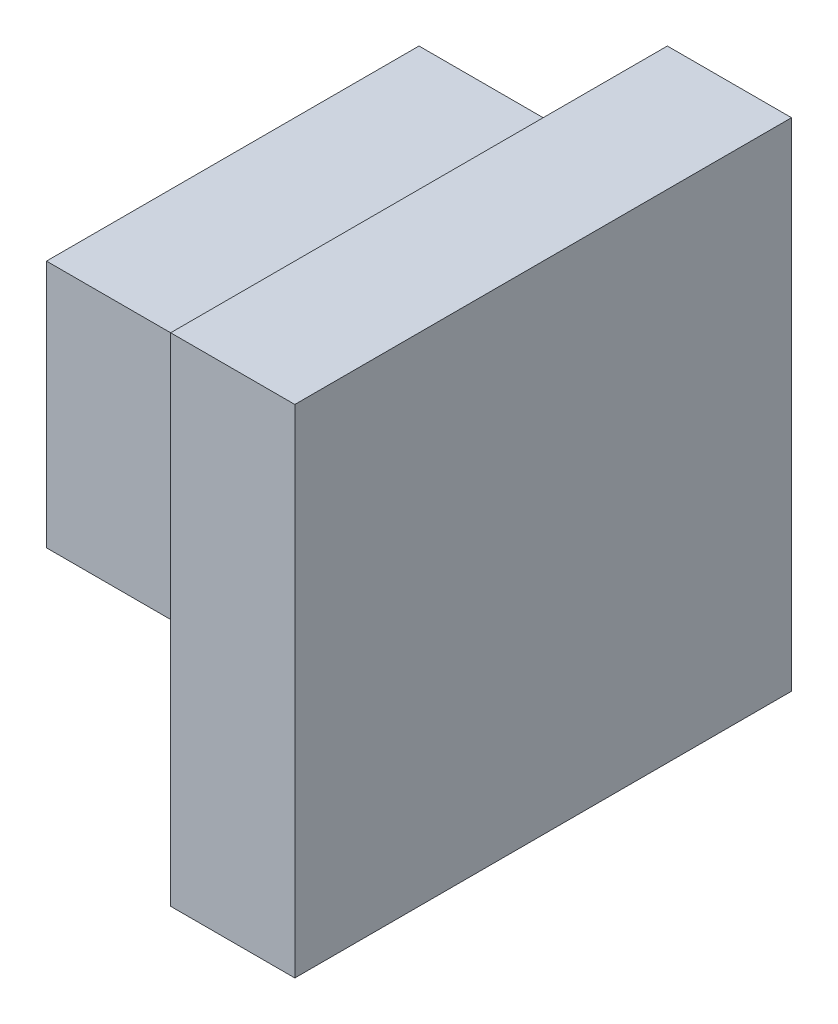
SolidWorks part; units mm, degrees
ref_plane "Front" through (0, 0, 0) normal (0, 0, 1) x (1, 0, 0)
ref_plane "Top" through (0, 0, 0) normal (0, 1, 0) x (1, 0, 0)
ref_plane "Right" through (0, 0, 0) normal (1, 0, 0) x (0, 0, -1)
sketch "Sketch1" plane through (0, 0, 0) normal (0, 0, 1) x (1, 0, 0)
  line L0 (0, 0) -> (0, 2)
  line L1 (0, 2) -> (1, 2)
  line L2 (1, 2) -> (1, 3)
  line L3 (1, 3) -> (3, 3)
  line L4 (3, 3) -> (3, 4)
  line L5 (3, 4) -> (4, 4)
  line L6 (4, 4) -> (4, 0)
  line L7 (4, 0) -> (3, 0)
  line L8 (3, 0) -> (3, 1)
  line L9 (3, 1) -> (1, 1)
  line L10 (1, 1) -> (1, 0)
  line L11 (1, 0) -> (0, 0)
  dimension "D1" = 4
  dimension "D2" = 1
  dimension "D3" = 1
  dimension "D4" = 1
  dimension "D5" = 1
  dimension "D6" = 2
  dimension "D7" = 1
  dimension "D8" = 1
  dimension "D9" = 2
extrude "Boss-Extrude1" add sketch "Sketch1" along normal blind 4
sketch "Sketch2" plane through (0, 0, 4) normal (0, 0, 1) x (1, 0, 0)
  line L5 (1, 3) -> (0, 3)
  line L6 (1, 3) -> (1, 0)
  line L7 (1, 0) -> (0, 0)
  line L8 (0, 3) -> (0, 0)
  point P6 (0, 0)
extrude "Cut-Extrude1" cut sketch "Sketch2" against normal blind 2
sketch "Sketch3" plane through (0, 0, 4) normal (0, 0, 1) x (1, 0, 0)
  line L1 (1, 3) -> (3, 3)
  line L2 (1, 3) -> (1, 0)
  line L3 (1, 0) -> (3, 0)
  line L4 (3, 3) -> (3, 0)
extrude "Cut-Extrude2" cut sketch "Sketch3" against normal blind 1
